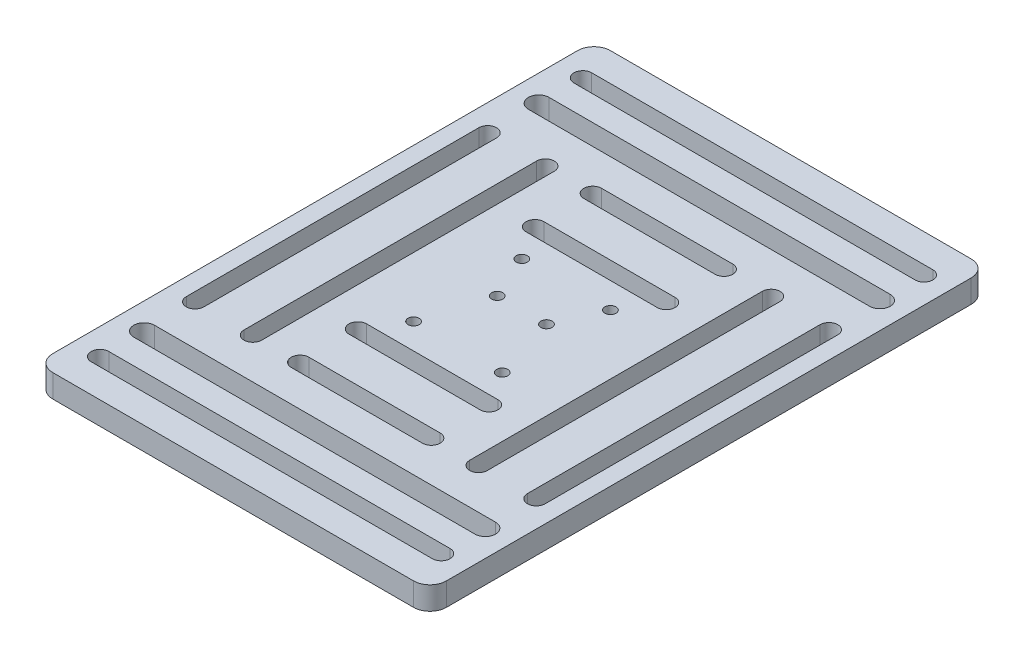
SolidWorks part; units mm, degrees
ref_plane "前视基准面" through (0, 0, 0) normal (0, 0, 1) x (1, 0, 0)
ref_plane "上视基准面" through (0, 0, 0) normal (0, 1, 0) x (1, 0, 0)
ref_plane "右视基准面" through (0, 0, 0) normal (1, 0, 0) x (0, 0, -1)
sketch "草图1" plane through (0, 0, 0) normal (0, 1, 0) x (1, 0, 0)
  line L0 (-55.2241, 16.5) -> (64.7759, 16.5) construction
  line L1 (-55.2241, 85) -> (64.7759, 85)
  line L2 (-55.2241, 85) -> (-55.2241, -85)
  line L3 (-55.2241, -85) -> (64.7759, -85)
  line L4 (64.7759, 85) -> (64.7759, -85)
  line L5 (64.7759, -52.4138) -> (-55.2241, -52.4138) construction
  line L6 (4.7759, 85) -> (4.7759, -85) construction
  line L7 (-8.7241, 85) -> (-8.7241, -85) construction
  line L8 (64.7759, 0) -> (-55.2241, 0) construction
  line L9 (-55.2241, 3) -> (64.7759, 3) construction
  line L10 (-2.7241, 8.233) -> (-2.7241, -8.0549) construction
  line L11 (-55.2241, 27) -> (64.7759, 27) construction
  line L12 (-55.2241, 44.6) -> (64.7759, 44.6) construction
  line L15 (-15.2241, 27) -> (24.7759, 27) construction
  line L16 (-15.2241, 29.7) -> (24.7759, 29.7)
  line L17 (-15.2241, 24.3) -> (24.7759, 24.3)
  line L18 (-15.2241, 44.6) -> (24.7759, 44.6) construction
  line L19 (-15.2241, 47.3) -> (24.7759, 47.3)
  line L20 (-15.2241, 41.9) -> (24.7759, 41.9)
  line L21 (-15.2241, -27) -> (24.7759, -27) construction
  line L22 (-15.2241, -29.7) -> (24.7759, -29.7)
  line L23 (-15.2241, -24.3) -> (24.7759, -24.3)
  line L24 (-15.2241, -44.6) -> (24.7759, -44.6) construction
  line L25 (-15.2241, -47.3) -> (24.7759, -47.3)
  line L26 (-15.2241, -41.9) -> (24.7759, -41.9)
  line L27 (-47.2241, 44.6) -> (-47.2241, -44.6) construction
  line L28 (-44.5241, 44.6) -> (-44.5241, -44.6)
  line L29 (-49.9241, 44.6) -> (-49.9241, -44.6)
  line L30 (-29.6241, 44.6) -> (-29.6241, -44.6) construction
  line L31 (-26.9241, 44.6) -> (-26.9241, -44.6)
  line L32 (-32.3241, 44.6) -> (-32.3241, -44.6)
  line L33 (39.1759, 44.6) -> (39.1759, -44.6) construction
  line L34 (36.4759, 44.6) -> (36.4759, -44.6)
  line L35 (41.8759, 44.6) -> (41.8759, -44.6)
  line L36 (56.7759, 44.6) -> (56.7759, -44.6) construction
  line L37 (54.0759, 44.6) -> (54.0759, -44.6)
  line L38 (59.4759, 44.6) -> (59.4759, -44.6)
  line L39 (56.7759, 60.1483) -> (-47.2241, 60.1483) construction
  line L40 (56.7759, 56.9975) -> (-47.2241, 56.9975)
  line L41 (56.7759, 63.2991) -> (-47.2241, 63.2991)
  line L42 (56.7759, 73.5907) -> (-47.2241, 73.5907) construction
  line L43 (56.7759, 70.8907) -> (-47.2241, 70.8907)
  line L44 (56.7759, 76.2907) -> (-47.2241, 76.2907)
  line L45 (56.7759, -60.1483) -> (-47.2241, -60.1483) construction
  line L46 (56.7759, -56.9975) -> (-47.2241, -56.9975)
  line L47 (56.7759, -63.2991) -> (-47.2241, -63.2991)
  line L48 (56.7759, -73.5907) -> (-47.2241, -73.5907) construction
  line L49 (56.7759, -70.8907) -> (-47.2241, -70.8907)
  line L50 (56.7759, -76.2907) -> (-47.2241, -76.2907)
  circle A0 centre (-8.7241, 16.5) radius 1.7
  circle A1 centre (18.2759, 16.5) radius 1.7
  circle A2 centre (18.2759, -16.5) radius 1.7
  circle A3 centre (-8.7241, -16.5) radius 1.7
  circle A4 centre (-2.7241, 3) radius 1.7
  circle A5 centre (12.2759, 3) radius 1.7
  arc A6 (-15.2241, 29.7) -> (-15.2241, 24.3) centre (-15.2241, 27) ccw
  arc A7 (24.7759, 24.3) -> (24.7759, 29.7) centre (24.7759, 27) ccw
  arc A8 (-15.2241, 47.3) -> (-15.2241, 41.9) centre (-15.2241, 44.6) ccw
  arc A9 (24.7759, 41.9) -> (24.7759, 47.3) centre (24.7759, 44.6) ccw
  arc A10 (-15.2241, -29.7) -> (-15.2241, -24.3) centre (-15.2241, -27) cw
  arc A11 (24.7759, -24.3) -> (24.7759, -29.7) centre (24.7759, -27) cw
  arc A12 (-15.2241, -47.3) -> (-15.2241, -41.9) centre (-15.2241, -44.6) cw
  arc A13 (24.7759, -41.9) -> (24.7759, -47.3) centre (24.7759, -44.6) cw
  arc A14 (-44.5241, 44.6) -> (-49.9241, 44.6) centre (-47.2241, 44.6) ccw
  arc A15 (-49.9241, -44.6) -> (-44.5241, -44.6) centre (-47.2241, -44.6) ccw
  arc A16 (-26.9241, 44.6) -> (-32.3241, 44.6) centre (-29.6241, 44.6) ccw
  arc A17 (-32.3241, -44.6) -> (-26.9241, -44.6) centre (-29.6241, -44.6) ccw
  arc A18 (36.4759, 44.6) -> (41.8759, 44.6) centre (39.1759, 44.6) cw
  arc A19 (41.8759, -44.6) -> (36.4759, -44.6) centre (39.1759, -44.6) cw
  arc A20 (54.0759, 44.6) -> (59.4759, 44.6) centre (56.7759, 44.6) cw
  arc A21 (59.4759, -44.6) -> (54.0759, -44.6) centre (56.7759, -44.6) cw
  arc A22 (56.7759, 56.9975) -> (56.7759, 63.2991) centre (56.7759, 60.1483) ccw
  arc A23 (-47.2241, 63.2991) -> (-47.2241, 56.9975) centre (-47.2241, 60.1483) ccw
  arc A24 (56.7759, 70.8907) -> (56.7759, 76.2907) centre (56.7759, 73.5907) ccw
  arc A25 (-47.2241, 76.2907) -> (-47.2241, 70.8907) centre (-47.2241, 73.5907) ccw
  arc A26 (56.7759, -56.9975) -> (56.7759, -63.2991) centre (56.7759, -60.1483) cw
  arc A27 (-47.2241, -63.2991) -> (-47.2241, -56.9975) centre (-47.2241, -60.1483) cw
  arc A28 (56.7759, -70.8907) -> (56.7759, -76.2907) centre (56.7759, -73.5907) cw
  arc A29 (-47.2241, -76.2907) -> (-47.2241, -70.8907) centre (-47.2241, -73.5907) cw
  point P37 (4.7759, 27)
  point P42 (4.7759, 44.6)
  point P49 (-47.2241, 0)
  point P53 (4.7759, -27)
  point P60 (4.7759, -44.6)
  point P70 (-29.6241, 0)
  point P79 (39.1759, 0)
  point P86 (56.7759, 0)
  point P93 (4.7759, 60.1483)
  point P98 (4.7759, 73.5907)
  point P107 (4.7759, -60.1483)
  point P114 (4.7759, -73.5907)
  dimension "D6" = 3.4
  dimension "D7" = 3
  dimension "D9" = 27
  dimension "D10" = 120
  dimension "D11" = 17.6
  dimension "D12" = 2.7
  dimension "D13" = 2.7
  dimension "D16" = 2.7
  dimension "D17" = 2.7
  dimension "D20" = 2.7
  dimension "D1" = 85
  dimension "D2" = 60
  dimension "D3" = 85
  dimension "D4" = 16.5
  dimension "D5" = 13.5
  dimension "D8" = 7.5
  dimension "D14" = 40
  dimension "D15" = 40
  dimension "D18" = 17.6
  dimension "D19" = 8
extrude "凸台-拉伸1" add sketch "草图1" along normal blind 7
sketch "草图3" plane through (0, 0, 0) normal (0, -1, 0) x (1, 0, 0)
  circle A0 centre (12.2759, -3) radius 3.4
  circle A1 centre (-2.7241, -3) radius 3.4
  circle A2 centre (18.2759, 16.5) radius 3.4
  circle A3 centre (-8.7241, 16.5) radius 3.4
  circle A4 centre (18.2759, -16.5) radius 3.4
  circle A5 centre (-8.7241, -16.5) radius 3.4
extrude "切除-拉伸1" cut sketch "草图3" against normal blind 3
fillet "圆角1" radius 5 4 edges at (64.7759, 3.5, 85) (-55.2241, 3.5, 85) (64.7759, 3.5, -85) (-55.2241, 3.5, -85)
sketch "草图4" plane through (0, 0, 0) normal (0, -1, 0) x (1, 0, 0)
  line L0 (64.7759, 0) -> (-55.2241, 0) construction
  line L1 (64.7759, 80) -> (64.7759, -80) construction
  line L2 (-55.2241, -80) -> (-55.2241, 80) construction
  line L3 (4.7759, -85) -> (4.7759, 85) construction
  line L4 (59.7759, -85) -> (-50.2241, -85) construction
  line L5 (-50.2241, 85) -> (59.7759, 85) construction
